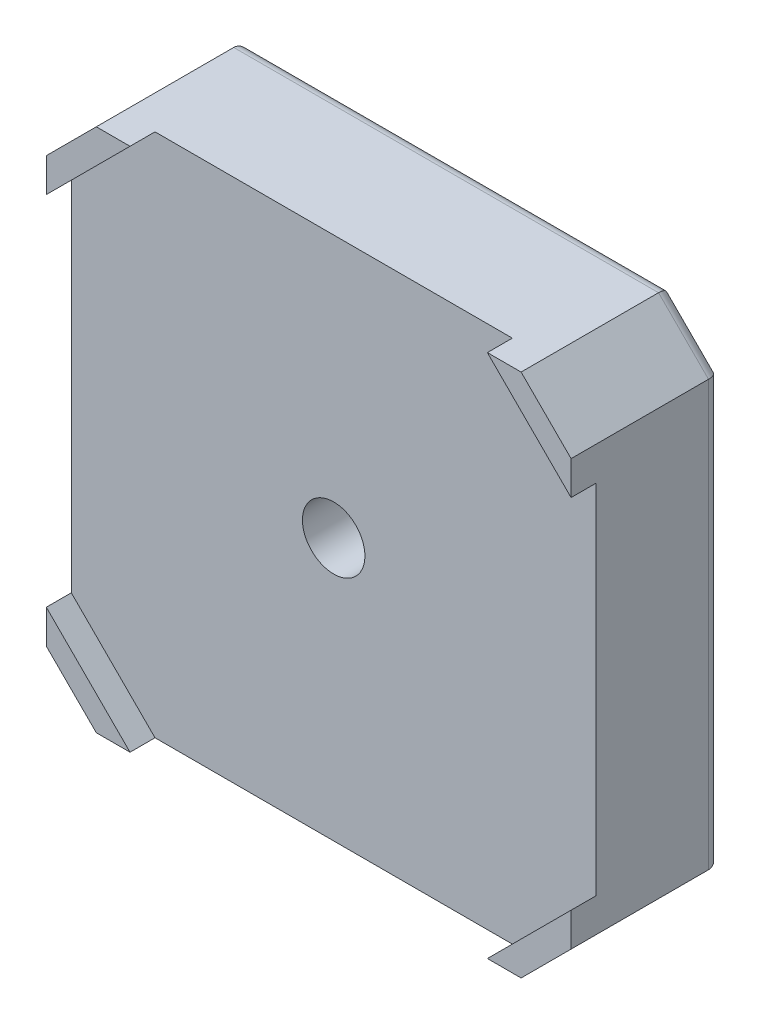
SolidWorks part; units mm, degrees
ref_plane "Front Plane" through (0, 0, 0) normal (0, 0, 1) x (1, 0, 0)
ref_plane "Top Plane" through (0, 0, 0) normal (0, 1, 0) x (1, 0, 0)
ref_plane "Right Plane" through (0, 0, 0) normal (1, 0, 0) x (0, 0, -1)
sketch "Sketch1" plane through (0, 0, 0) normal (0, 0, 1) x (1, 0, 0)
  line L0 (-21, 17) -> (-17, 21)
  line L1 (-17, -21) -> (17, -21)
  line L2 (-21, -17) -> (-21, 17)
  line L3 (-17, 21) -> (17, 21)
  line L4 (21, -17) -> (21, 17)
  line L5 (-21, -21) -> (21, 21) construction
  line L6 (-21, 21) -> (21, -21) construction
  line L7 (17, 21) -> (21, 17)
  line L8 (17, -21) -> (21, -17)
  line L9 (-21, -17) -> (-17, -21)
  point P0 (0, 0)
  dimension "D1" = 42
extrude "Boss-Extrude1" add sketch "Sketch1" along normal blind 12
sketch "Sketch2" plane through (0, 0, 12) normal (0, 0, 1) x (1, 0, 0)
  line L0 (-21.15, 14.15) -> (-14.15, 21.15)
  line L1 (-14.15, -21.15) -> (14.15, -21.15)
  line L2 (-21.15, -14.15) -> (-21.15, 14.15)
  line L3 (-14.15, 21.15) -> (14.15, 21.15)
  line L4 (21.15, -14.15) -> (21.15, 14.15)
  line L5 (-21.15, -21.15) -> (21.15, 21.15) construction
  line L6 (-21.15, 21.15) -> (21.15, -21.15) construction
  line L7 (14.15, 21.15) -> (21.15, 14.15)
  line L8 (14.15, -21.15) -> (21.15, -14.15)
  line L9 (-21.15, -14.15) -> (-14.15, -21.15)
  point P0 (0, 0)
  dimension "D1" = 42.3
  dimension "D2" = 42.3
extrude "Cut-Extrude1" cut sketch "Sketch2" against normal blind 2
sketch "Sketch3" plane through (0, 0, 0) normal (0, 0, -1) x (-1, 0, 0)
  circle A0 centre (0, 0) radius 11
  dimension "D1" = 22
extrude "Boss-Extrude2" add sketch "Sketch3" along normal blind 2
sketch "Sketch4" plane through (0, 0, -2) normal (0, 0, -1) x (-1, 0, 0)
  circle A0 centre (0, 0) radius 5.5
  dimension "D1" = 11
extrude "Cut-Extrude2" cut sketch "Sketch4" against normal blind 7
sketch "Sketch5" plane through (0, 0, 5) normal (0, 0, -1) x (-1, 0, 0)
  circle A0 centre (0, 0) radius 2.5
  dimension "D1" = 5
extrude "Cut-Extrude3" cut sketch "Sketch5" against normal through all
fillet "Fillet1" radius 1 8 edges at (-19, 19, 0) (-21, 0, 0) (-19, -19, 0) (0, -21, 0) (19, -19, 0) (21, 0, 0) (19, 19, 0) (0, 21, 0)
fillet "Fillet2" radius 0.5 3 edges at (-11, 0, -2) (-5.5, 0, -2) (-5.5, 0, 5)
hole_wizard "M3x0.5 Tapped Hole1" positions "Sketch7" profile "Sketch8" tap size "M3x0.5" standard "ANSI Metric"
sketch "Sketch7" plane through (0, 0, 0) normal (0, 0, -1) x (-1, 0, 0)
  line L1 (-15.5, -15.5) -> (15.5, -15.5) construction
  line L2 (-15.5, -15.5) -> (-15.5, 15.5) construction
  line L3 (-15.5, 15.5) -> (15.5, 15.5) construction
  line L4 (15.5, -15.5) -> (15.5, 15.5) construction
  line L5 (-15.5, -15.5) -> (15.5, 15.5) construction
  line L6 (-15.5, 15.5) -> (15.5, -15.5) construction
  point P0 (-15.5, 15.5)
  point P2 (15.5, 15.5)
  point P5 (0, 0)
  point P250 (-15.5, 15.5)
  point P251 (15.5, 15.5)
  dimension "D1" = 31
sketch "Sketch8" plane through (15.5, 15.5, 0) normal (1, 0, 0) x (0, 1, 0)
  line L0 (0, 0) -> (0, 5.2511)
  line L1 (0, 5.2511) -> (1.25, 4.5)
  line L2 (1.25, 4.5) -> (1.25, 0)
  line L5 (1.25, 0) -> (0, 0)
  line L10 (0, 5.2511) -> (-1.25, 4.5) construction
  line L11 (0, -6.35) -> (0, 107.95) construction
  dimension "Tap Drill Dia." = 2.5
  dimension "Tap Drill Depth" = 4.5
  dimension "Drill Angle" = 118
cosmetic thread "Hole Thread1" parameters "D1"=6, "D2"=3
cosmetic thread "Hole Thread2" parameters "D1"=6, "D2"=3
pattern_linear "LPattern1" count 2 spacing 31 along (0, -1, 0) of "M3x0.5 Tapped Hole1"
cosmetic thread "Hole Thread3" parameters "D1"=6, "D2"=3
cosmetic thread "Hole Thread4" parameters "D1"=6, "D2"=3
fillet "Fillet4" radius 0.25 4 edges at (14.25, -15.5, 0) (-16.75, -15.5, 0) (-16.75, 15.5, 0) (14.25, 15.5, 0)
